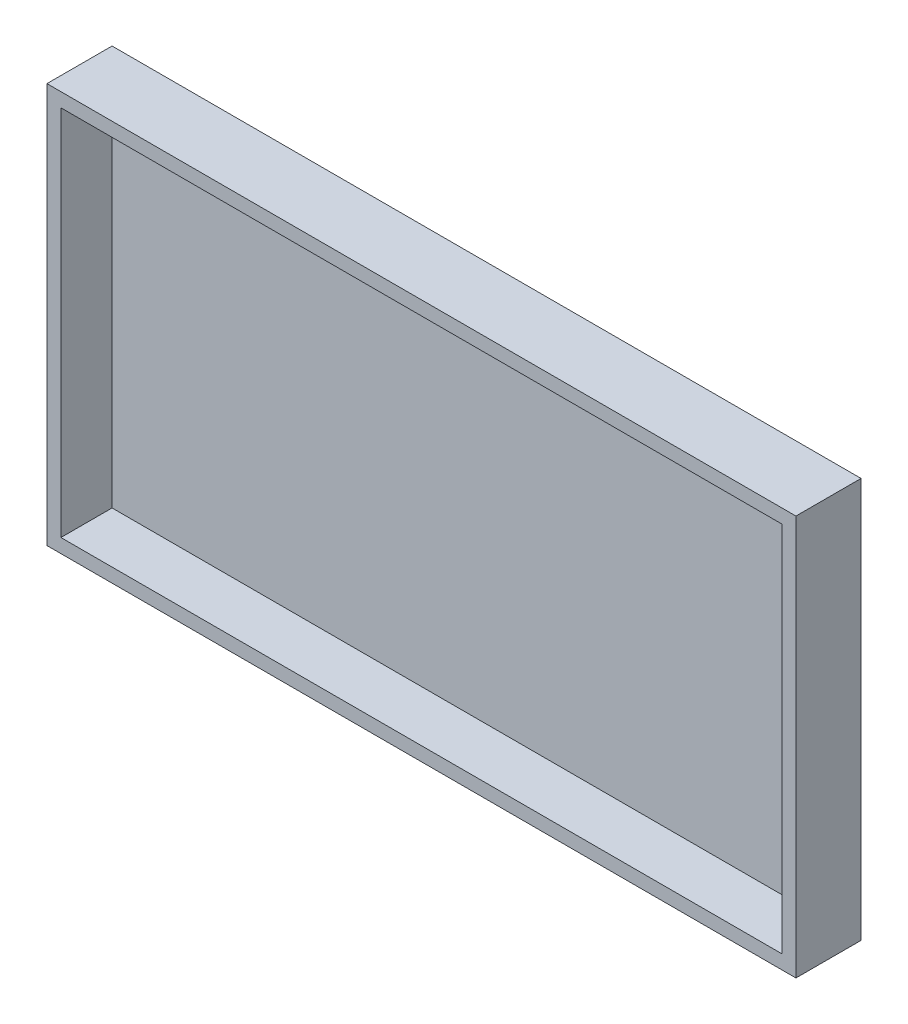
SolidWorks part; units mm, degrees
ref_plane "前基準面" through (0, 0, 0) normal (0, 0, 1) x (1, 0, 0)
ref_plane "上基準面" through (0, 0, 0) normal (0, 1, 0) x (1, 0, 0)
ref_plane "右基準面" through (0, 0, 0) normal (1, 0, 0) x (0, 0, -1)
sketch "草圖1" plane through (0, 0, 0) normal (0, 0, 1) x (1, 0, 0)
  line L1 (-59.7769, 24.8878) -> (101.2231, 24.8878)
  line L2 (-59.7769, 24.8878) -> (-59.7769, -61.1122)
  line L3 (-59.7769, -61.1122) -> (101.2231, -61.1122)
  line L4 (101.2231, 24.8878) -> (101.2231, -61.1122)
  dimension "D1" = 161
  dimension "D2" = 86
extrude "填料-伸長2" add sketch "草圖1" along normal blind 14
sketch "草圖2" plane through (0, 0, 14) normal (0, 0, 1) x (1, 0, 0)
  line L0 (101.2231, 24.8878) -> (-59.7769, 24.8878) construction
  line L1 (-56.7769, 21.8878) -> (98.2231, 21.8878)
  line L2 (-56.7769, 21.8878) -> (-56.7769, -58.1122)
  line L3 (-56.7769, -58.1122) -> (98.2231, -58.1122)
  line L4 (98.2231, 21.8878) -> (98.2231, -58.1122)
  line L5 (-59.7769, 24.8878) -> (-59.7769, -61.1122) construction
  line L6 (-59.7769, -61.1122) -> (101.2231, -61.1122) construction
  line L7 (101.2231, -61.1122) -> (101.2231, 24.8878) construction
  dimension "D1" = 3
  dimension "D2" = 3
  dimension "D3" = 3
  dimension "D4" = 3
extrude "除料-伸長1" cut sketch "草圖2" against normal blind 11
